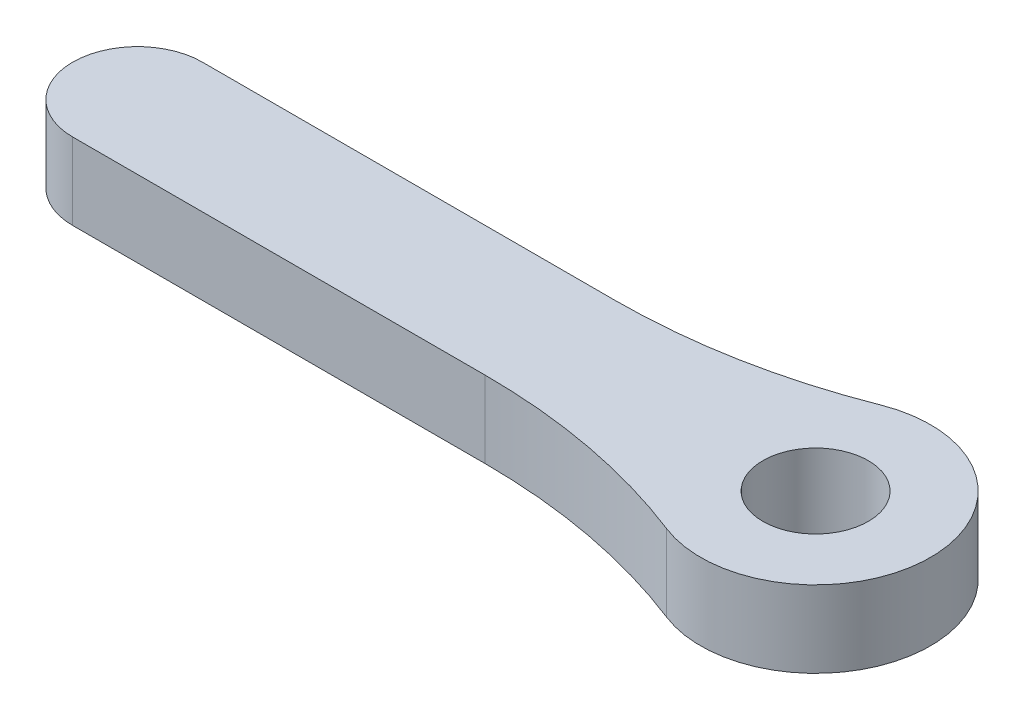
SolidWorks part; units mm, degrees
ref_plane "Front Plane" through (0, 0, 0) normal (0, 0, 1) x (1, 0, 0)
ref_plane "Top Plane" through (0, 0, 0) normal (0, 1, 0) x (1, 0, 0)
ref_plane "Right Plane" through (0, 0, 0) normal (1, 0, 0) x (0, 0, -1)
sketch "Sketch1" plane through (0, 0, 0) normal (0, 1, 0) x (1, 0, 0)
  line L0 (0, 0) -> (-25.4, 0) construction
  line L1 (-3.9329, -2.6859) -> (-25.4, -2.6859)
  line L2 (-3.9329, 2.6859) -> (-25.4, 2.6859)
  line L3 (-25.4, 2.6859) -> (-28.0859, 2.6859)
  line L4 (-28.0859, -2.6859) -> (-25.4, -2.6859)
  arc A0 (-28.0859, 2.6859) -> (-28.0859, -2.6859) centre (-28.0859, 0) ccw
  arc A2 (-3.9329, -2.6859) -> (-3.9329, 2.6859) centre (0, 0) ccw
  point P3 (-12.7, 0)
  dimension "D1" = 25.4
extrude "Boss-Extrude1" add sketch "Sketch1" along normal blind 3.175
hole_wizard "11/64 (0.17188) Diameter Hole1" positions "Sketch3" profile "Sketch2" hole size "11/64" standard "ANSI Inch" end condition through all
sketch "Sketch3" plane through (0, 3.175, 0) normal (0, 1, 0) x (1, 0, 0)
  point P0 (0, 0)
sketch "Sketch2" plane through (0, 3.175, 0) normal (1, 0, 0) x (0, 0, 1)
  line L0 (0, 0) -> (0, 3.175)
  line L1 (0, 3.175) -> (2.1829, 3.175)
  line L2 (2.1829, 3.175) -> (2.1829, 0)
  line L5 (2.1829, 0) -> (0, 0)
  line L11 (0, -6.35) -> (0, 107.95) construction
  dimension "Thru Hole Dia." = 4.3658
  dimension "Thru Hole Depth" = 3.175
fillet "Fillet1" radius 25.4 2 edges at (-3.9329, 1.5875, -2.6859) (-3.9329, 1.5875, 2.6859)
